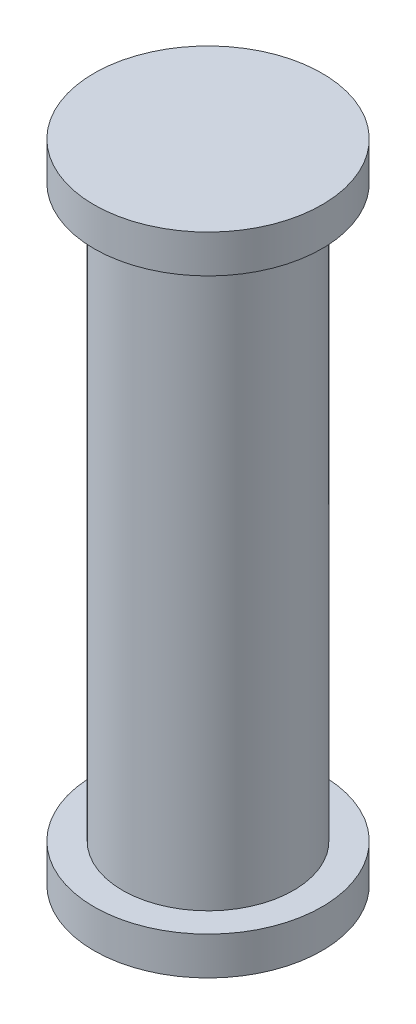
SolidWorks part; units mm, degrees
ref_plane "Front Plane" through (0, 0, 0) normal (0, 0, 1) x (1, 0, 0)
ref_plane "Top Plane" through (0, 0, 0) normal (0, 1, 0) x (1, 0, 0)
ref_plane "Right Plane" through (0, 0, 0) normal (1, 0, 0) x (0, 0, -1)
sketch "Sketch1" plane through (0, 0, 0) normal (0, 1, 0) x (1, 0, 0)
  circle A0 centre (0, 0) radius 4.5
extrude "Boss-Extrude1" add sketch "Sketch1" along normal blind 30
sketch "Sketch2" plane through (0, 0, 0) normal (0, 1, 0) x (1, 0, 0)
  circle A0 centre (0, 0) radius 6
extrude "Boss-Extrude2" add sketch "Sketch2" against normal blind 2
sketch "Sketch3" plane through (0, 30, 0) normal (0, 1, 0) x (1, 0, 0)
  circle A0 centre (0, 0) radius 6
extrude "Boss-Extrude3" add sketch "Sketch3" along normal blind 2
